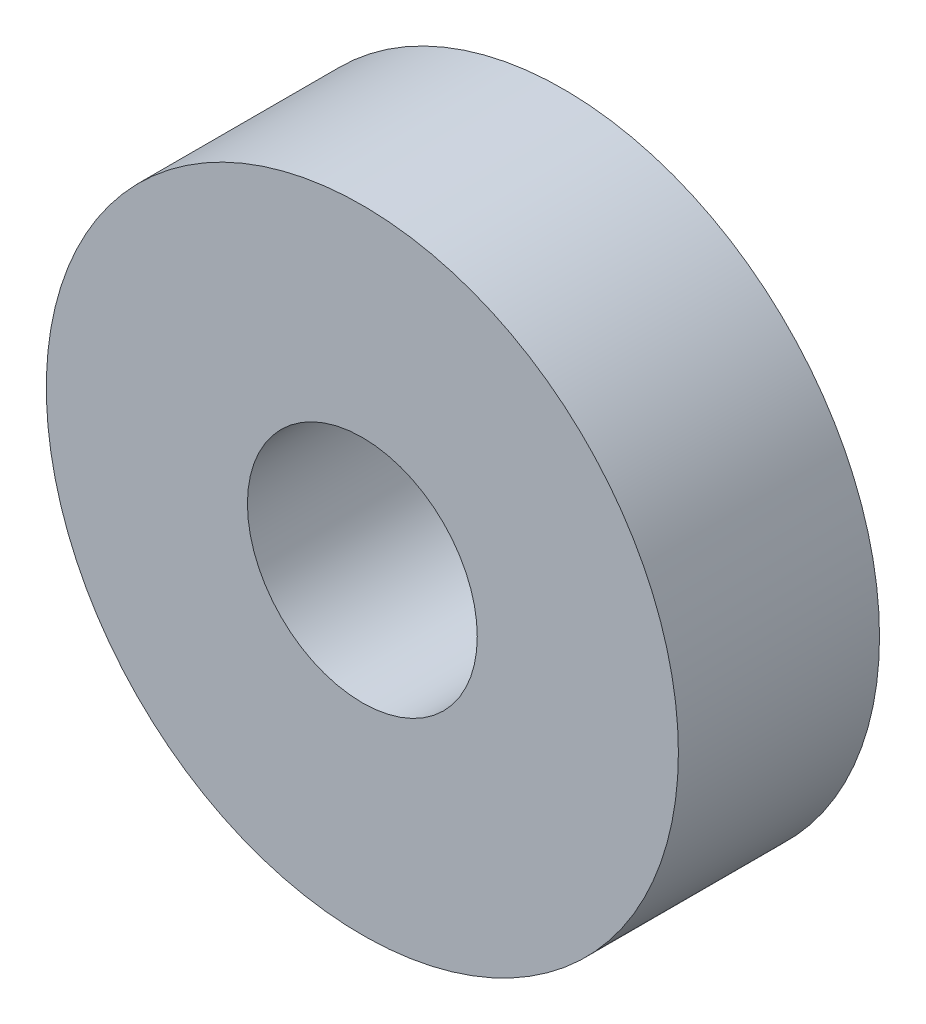
SolidWorks part; units mm, degrees
ref_plane "Front Plane" through (0, 0, 0) normal (0, 0, 1) x (1, 0, 0)
ref_plane "Top Plane" through (0, 0, 0) normal (0, 1, 0) x (1, 0, 0)
ref_plane "Right Plane" through (0, 0, 0) normal (1, 0, 0) x (0, 0, -1)
sketch "Sketch1" plane through (0, 0, 0) normal (0, 0, 1) x (1, 0, 0)
  circle A0 centre (0, 0) radius 11
  circle A1 centre (0, 0) radius 4
extrude "Boss-Extrude1" add sketch "Sketch1" along normal blind 7
